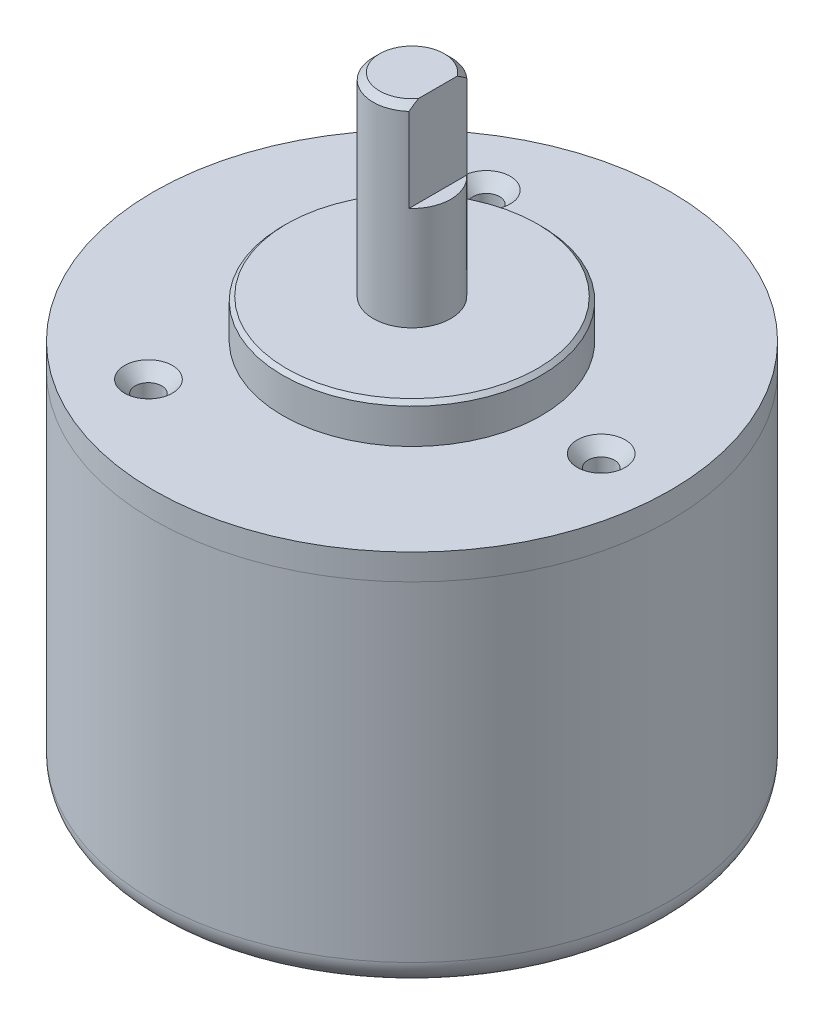
SolidWorks part; units mm, degrees
ref_plane "Alzado" through (0, 0, 0) normal (0, 0, 1) x (1, 0, 0)
ref_plane "Planta" through (0, 0, 0) normal (0, 1, 0) x (1, 0, 0)
ref_plane "Vista lateral" through (0, 0, 0) normal (1, 0, 0) x (0, 0, -1)
sketch "Croquis1" plane through (0, 0, 0) normal (0, 1, 0) x (1, 0, 0)
  circle A0 centre (0, 0) radius 20
extrude "Saliente-Extruir1" add sketch "Croquis1" along normal blind 2
sketch "Croquis2" plane through (0, 2, 0) normal (0, 1, 0) x (1, 0, 0)
  circle A0 centre (0, 0) radius 10
extrude "Saliente-Extruir2" add sketch "Croquis2" along normal blind 3
sketch "Croquis3" plane through (0, 5, 0) normal (0, 1, 0) x (1, 0, 0)
  circle A0 centre (0, 0) radius 3
extrude "Saliente-Extruir3" add sketch "Croquis3" along normal blind 15
chamfer "Chaflán1" distance 0.5 angle 45 1 edges at (0, 20, 3)
chamfer "Chaflán2" distance 0.3 angle 45 1 edges at (0, 5, 10)
sketch "Croquis4" plane through (0, 0, 0) normal (0, -1, 0) x (1, 0, 0)
  circle A0 centre (0, 0) radius 20
extrude "Saliente-Extruir4" add sketch "Croquis4" along normal blind 27.5 separate body
fillet "Redondeo1" radius 2 1 edges at (0, -27.5, -20)
sketch "Croquis6" plane through (0, 20, 0) normal (0, 1, 0) x (1, 0, 0)
  line L1 (2, 0) -> (2, -3)
  line L2 (2, -3) -> (4, -3)
  line L3 (4, -3) -> (4, 3)
  line L4 (4, 3) -> (2, 3)
  line L5 (2, 3) -> (2, 0)
  dimension "D1" = 2
  dimension "D2" = 6
  dimension "D3" = 4
  dimension "D4" = 3
extrude "Cortar-Extruir2" cut sketch "Croquis6" against normal blind 7
hole_wizard "Avellanado para tornillo con cabeza ovalada de #11" positions "Croquis3D3" profile "Croquis9" countersink size "#1" standard "Ansi Inch"
sketch3d "Croquis3D3"
  line L0 (0, 0, 0) -> (0, 29.5237, 0) construction
  point P0 (14.8644, 2, 0.226)
  dimension "D1" = 15
sketch "Croquis9" plane through (14.8644, 2, 0.226) normal (1, 0, 0) x (0, 0, 1)
  line L0 (0, 0) -> (0, 10.6181)
  line L1 (0, 10.6181) -> (1.0287, 10)
  line L2 (1.0287, 10) -> (1.0287, 0.9496)
  line L3 (1.0287, 0.9496) -> (1.8542, 0)
  line L5 (1.8542, 0) -> (0, 0)
  line L6 (-1.0287, 0.9496) -> (-1.8542, 0) construction
  line L10 (0, 10.6181) -> (-1.0287, 10) construction
  line L11 (0, -6.35) -> (0, 107.95) construction
  dimension "Diámetro de taladro" = 2.0574
  dimension "Profundidad de taladro" = 10
  dimension "Ángulo de avellanado cercano" = 3.7084
  dimension "Ángulo de avellanado lejano" = 82
  dimension "Ángulo de perforador" = 118
pattern_circular "MatrizC8" count 3 over 360 about axis through (0, 0, 0) along (0, 1, 0) of "Avellanado para tornillo con cabeza ovalada de #11"
